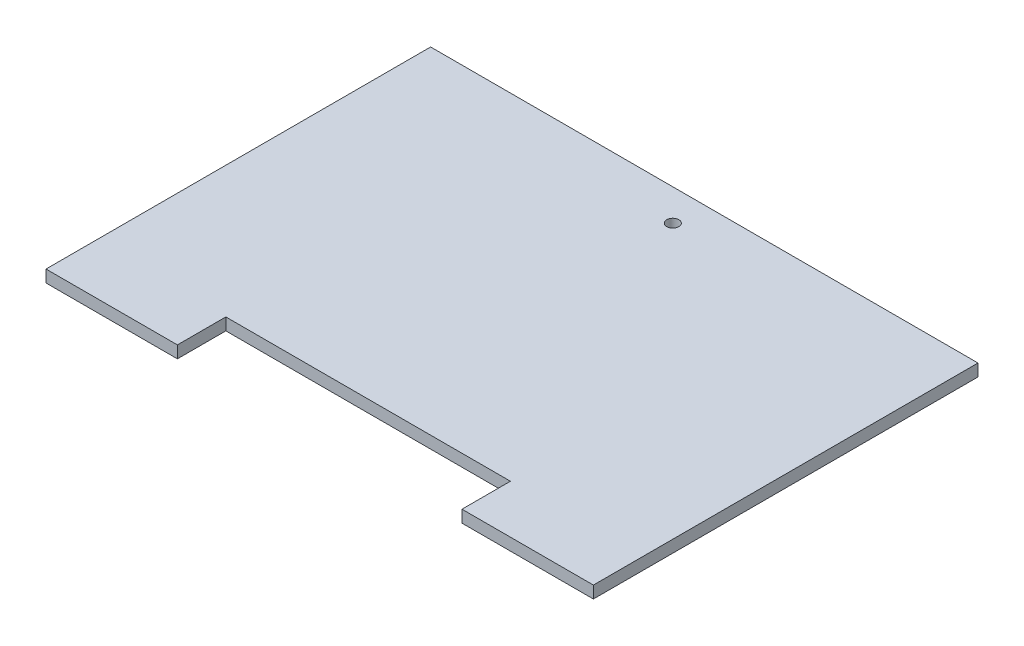
SolidWorks part; units mm, degrees
material "PC High Viscosity"
ref_plane "Front Plane" through (0, 0, 0) normal (0, 0, 1) x (1, 0, 0)
ref_plane "Top Plane" through (0, 0, 0) normal (0, 1, 0) x (1, 0, 0)
ref_plane "Right Plane" through (0, 0, 0) normal (1, 0, 0) x (0, 0, -1)
sketch "Sketch1" plane through (0, 0, 0) normal (0, 1, 0) x (1, 0, 0)
  line L1 (-143.51, 100.838) -> (143.51, 100.838)
  line L2 (-143.51, 100.838) -> (-143.51, -100.838)
  line L3 (-143.51, -100.838) -> (143.51, -100.838)
  line L4 (143.51, 100.838) -> (143.51, -100.838)
  line L5 (-143.51, 100.838) -> (143.51, -100.838) construction
  line L6 (-143.51, -100.838) -> (143.51, 100.838) construction
  point P0 (0, 0)
  dimension "D1" = 287.02
  dimension "D2" = 201.676
extrude "Boss-Extrude1" add sketch "Sketch1" along normal mid plane 6.35
sketch "Sketch2" plane through (0, 3.175, 0) normal (0, 1, 0) x (1, 0, 0)
  line L0 (-106.807, -100.838) -> (-106.807, -81.788) construction
  line L1 (-143.51, -100.838) -> (143.51, -100.838) construction
  line L2 (-100.457, -75.438) -> (-59.182, -75.438) construction
  line L3 (-52.832, -81.788) -> (-52.832, -100.838) construction
  line L4 (-52.832, -100.838) -> (-106.807, -100.838) construction
  line L5 (0, -246.692) -> (0, 213.8077) construction
  line L6 (52.832, -100.838) -> (106.807, -100.838) construction
  line L7 (52.832, -81.788) -> (52.832, -100.838) construction
  line L8 (100.457, -75.438) -> (59.182, -75.438) construction
  line L9 (106.807, -100.838) -> (106.807, -81.788) construction
  line L10 (-74.6125, -100.838) -> (-74.6125, -75.438)
  line L11 (-143.51, 100.838) -> (-143.51, -100.838) construction
  line L12 (-74.6125, -75.438) -> (74.6125, -75.438)
  line L13 (74.6125, -75.438) -> (74.6125, -100.838)
  line L14 (74.6125, -100.838) -> (-74.6125, -100.838)
  arc A0 (100.457, -75.438) -> (106.807, -81.788) centre (100.457, -81.788) cw construction
  arc A1 (52.832, -81.788) -> (59.182, -75.438) centre (59.182, -81.788) cw construction
  arc A2 (-59.182, -75.438) -> (-52.832, -81.788) centre (-59.182, -81.788) cw construction
  arc A3 (-106.807, -81.788) -> (-100.457, -75.438) centre (-100.457, -81.788) cw construction
  point P17 (106.807, -75.438)
  point P20 (52.832, -75.438)
  point P23 (-52.832, -75.438)
  point P26 (-106.807, -75.438)
  dimension "D4" = 6.35
  dimension "D1" = 25.4
  dimension "D2" = 53.975
  dimension "D3" = 36.703
  dimension "D5" = 149.225
extrude "Cut-Extrude1" cut sketch "Sketch2" against normal through all both and the other way through all
sketch "Sketch3" plane through (0, -3.175, 0) normal (0, -1, 0) x (1, 0, 0)
  line L0 (-143.51, 88.138) -> (143.51, 88.138) construction
  line L1 (-143.51, -100.838) -> (-143.51, 100.838) construction
  line L2 (143.51, 100.838) -> (143.51, -100.838) construction
  line L5 (143.51, -100.838) -> (-143.51, -100.838) construction
  line L7 (-143.51, 100.838) -> (-74.6125, 100.838) construction
  line L8 (0, 164.6765) -> (0, -174.0667) construction
  circle A1 centre (41.91, 88.138) radius 3.175
  circle A4 centre (0, -84.328) radius 3.175
  circle A5 centre (-41.91, 88.138) radius 3.175
  dimension "D1" = 6.35
  dimension "D2" = 12.7
  dimension "D5" = 101.6
  dimension "D7" = 6.35
  dimension "D8" = 16.51
extrude "Cut-Extrude2" cut sketch "Sketch3" against normal through all both and the other way through all
sketch "Sketch4" [suppressed] plane through (0, -3.175, 0) normal (0, -1, 0) x (1, 0, 0)
  line L0 (-76.2, 74.93) -> (76.2, 74.93) construction
  line L1 (-76.2, 113.03) -> (76.2, 113.03)
  line L2 (-76.2, 36.83) -> (76.2, 36.83)
  line L4 (-63.5, -68.58) -> (63.5, -68.58)
  line L5 (-76.2, -81.28) -> (-76.2, -106.68)
  line L6 (-63.5, -119.38) -> (63.5, -119.38)
  line L7 (76.2, -81.28) -> (76.2, -106.68)
  line L9 (-152.4, 144.78) -> (152.4, 144.78) construction
  line L10 (152.4, -144.78) -> (-152.4, -144.78) construction
  arc A0 (-76.2, 113.03) -> (-76.2, 36.83) centre (-76.2, 74.93) ccw
  arc A1 (76.2, 36.83) -> (76.2, 113.03) centre (76.2, 74.93) ccw
  circle A2 centre (0, -45.72) radius 4.7625
  arc A3 (63.5, -68.58) -> (76.2, -81.28) centre (63.5, -81.28) cw
  arc A4 (63.5, -119.38) -> (76.2, -106.68) centre (63.5, -106.68) ccw
  arc A5 (-76.2, -106.68) -> (-63.5, -119.38) centre (-63.5, -106.68) ccw
  arc A6 (-63.5, -68.58) -> (-76.2, -81.28) centre (-63.5, -81.28) ccw
  circle A7 centre (44.323, -39.37) radius 1.5875
  circle A8 centre (44.323, -52.07) radius 1.5875
  circle A9 centre (92.71, -52.07) radius 1.5875
  circle A10 centre (92.71, -39.37) radius 1.5875
  circle A11 centre (141.097, -39.37) radius 1.5875
  circle A12 centre (141.097, -52.07) radius 1.5875
  point P2 (0, 74.93)
  point P21 (0, -68.58)
  point P22 (0, 113.03)
  point P25 (0, -119.38)
  dimension "D1" = 12.7
  dimension "D5" = 9.525
  dimension "D10" = 3.175
  dimension "D2" = 190.5
  dimension "D3" = 76.2
  dimension "D4" = 50.8
  dimension "D6" = 25.4
  dimension "D7" = 152.4
  dimension "D8" = 127
  dimension "D9" = 31.75
extrude "Cut-Extrude3" [suppressed] cut sketch "Sketch4" against normal through all both and the other way through all
sketch "Sketch5" [suppressed] plane through (0, -3.175, 0) normal (0, -1, 0) x (1, 0, 0)
  line L0 (109.855, -144.78) -> (-109.855, -144.78) construction
  line L2 (109.855, 144.78) -> (109.855, -144.78) construction
  circle A0 centre (97.155, -93.98) radius 6.35
  dimension "D3" = 12.7
  dimension "D1" = 98.425
  dimension "D2" = 12.7
extrude "Cut-Extrude4" [suppressed] cut sketch "Sketch5" against normal through all both and the other way through all
sketch "Sketch6" plane through (0, -3.175, 0) normal (0, 1, 0) x (1, 0, 0)
  line L14 (74.6125, -100.838) -> (74.6125, -75.438) construction
  line L15 (-74.6125, -75.438) -> (-74.6125, -100.838) construction
  line L16 (74.6125, -75.438) -> (-74.6125, -75.438) construction
  line L17 (74.6125, -100.838) -> (74.6125, -75.438)
  line L18 (-74.6125, -75.438) -> (-74.6125, -100.838)
  line L19 (74.6125, -75.438) -> (-74.6125, -75.438)
  line L20 (-74.6125, -100.838) -> (74.6125, -100.838)
extrude "Boss-Extrude2" [suppressed] add sketch "Sketch6" along normal blind 2.794
sketch "Sketch7" [suppressed] plane through (0, 3.175, 0) normal (0, 1, 0) x (1, 0, 0)
  line L1 (136.525, -143.51) -> (136.525, 143.51) construction
  circle A0 centre (111.125, 0) radius 3.175
  dimension "D1" = 6.35
  dimension "D2" = 25.4
extrude "Cut-Extrude5" [suppressed] cut sketch "Sketch7" against normal through all both and the other way through all
